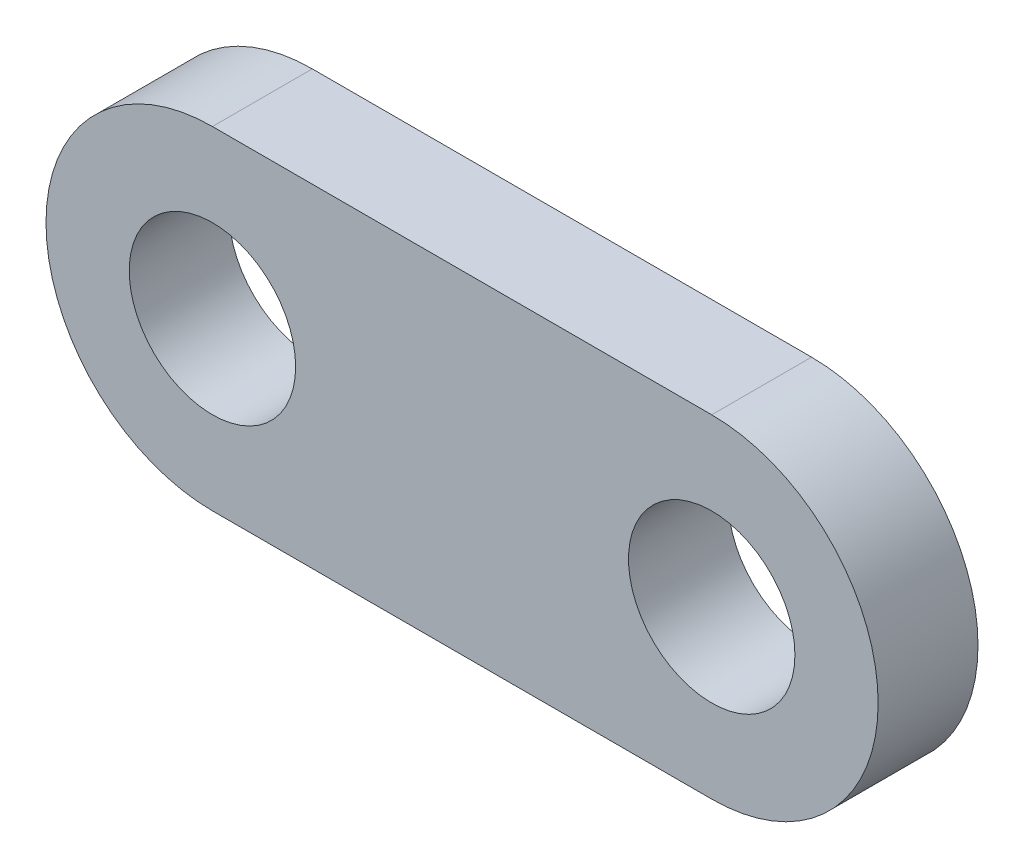
SolidWorks part; units mm, degrees
ref_plane "Front Plane" through (0, 0, 0) normal (0, 0, 1) x (1, 0, 0)
ref_plane "Top Plane" through (0, 0, 0) normal (0, 1, 0) x (1, 0, 0)
ref_plane "Right Plane" through (0, 0, 0) normal (1, 0, 0) x (0, 0, -1)
sketch "Sketch1" plane through (0, 0, 0) normal (0, 0, 1) x (1, 0, 0)
  line L0 (-7.5, 0) -> (7.5, 0) construction
  line L1 (-7.5, 5) -> (7.5, 5)
  line L2 (-7.5, -5) -> (7.5, -5)
  arc A0 (-7.5, 5) -> (-7.5, -5) centre (-7.5, 0) ccw
  arc A1 (7.5, -5) -> (7.5, 5) centre (7.5, 0) ccw
  circle A2 centre (7.5, 0) radius 2.5
  circle A3 centre (-7.5, 0) radius 2.5
  point P2 (0, 0)
  dimension "D1" = 5
  dimension "D3" = 5
  dimension "D2" = 15
extrude "Boss-Extrude1" add sketch "Sketch1" along normal blind 3
